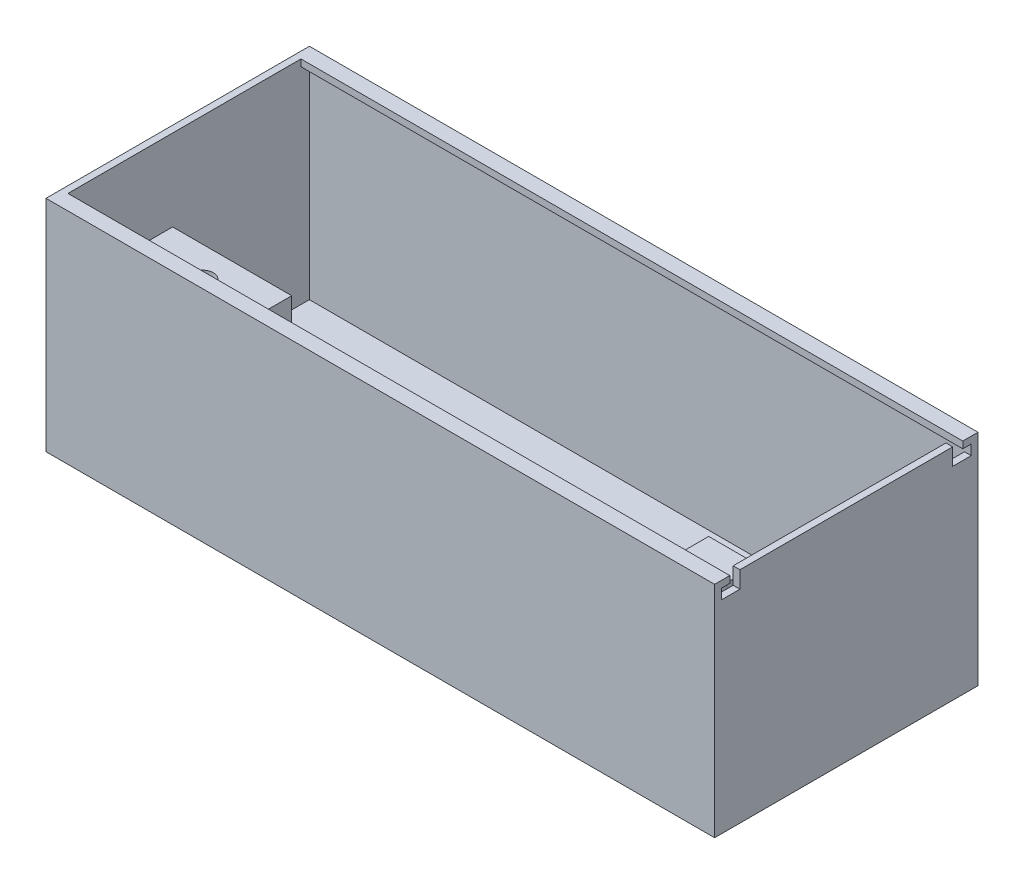
SolidWorks part; units mm, degrees
material "ABS"
ref_plane "Front" through (0, 0, 0) normal (0, 0, 1) x (1, 0, 0)
ref_plane "Top" through (0, 0, 0) normal (0, 1, 0) x (1, 0, 0)
ref_plane "Right" through (0, 0, 0) normal (1, 0, 0) x (0, 0, -1)
sketch "Sketch2" plane through (0, 0, 0) normal (0, 1, 0) x (1, 0, 0)
  line L1 (-99, -39) -> (99, -39)
  line L2 (-99, -39) -> (-99, 39)
  line L3 (-99, 39) -> (99, 39)
  line L4 (99, -39) -> (99, 39)
  line L5 (-99, -39) -> (99, 39) construction
  line L6 (-99, 39) -> (99, -39) construction
  point P0 (0, 0)
  dimension "D1" = 78
  dimension "D2" = 198
extrude "Boss-Extrude1" add sketch "Sketch2" along normal blind 50 and the other way blind 15
shell "Shell1" thickness 2
fillet "Fillet1" [suppressed] radius 10
sketch "Sketch3" plane through (-97, 0, 0) normal (1, 0, 0) x (0, 0, -1)
  line L0 (0, -15) -> (0, 50) construction
  line L1 (-37, 50) -> (-34.5, 50)
  line L2 (-37, 50) -> (-37, 48)
  line L3 (-37, 48) -> (-34.5, 48)
  line L4 (-34.5, 50) -> (-34.5, 48)
  line L5 (39, -15) -> (-39, -15) construction
  line L6 (37, 50) -> (-37, 50) construction
  line L7 (34.5, 50) -> (34.5, 48)
  line L8 (37, 48) -> (34.5, 48)
  line L9 (37, 50) -> (37, 48)
  line L10 (37, 50) -> (34.5, 50)
  dimension "D1" = 2.5
  dimension "D2" = 2
extrude "Boss-Extrude2" add sketch "Sketch3" along normal up to next
sketch "Sketch4" plane through (97, 0, 0) normal (-1, 0, 0) x (0, 0, 1)
  line L0 (-37, 48) -> (-37, 45)
  line L1 (-37, 48) -> (-37, -13) construction
  line L2 (-37, 45) -> (-31.5, 45)
  line L3 (-31.5, 45) -> (-31.5, 50)
  line L4 (34.5, 50) -> (-34.5, 50) construction
  line L5 (-31.5, 50) -> (-34.5, 50)
  line L6 (-34.5, 50) -> (-34.5, 48)
  line L7 (-37, 48) -> (-34.5, 48) construction
  line L8 (-34.5, 48) -> (-34.5, 50) construction
  line L9 (-34.5, 48) -> (-37, 48)
  line L10 (0, -15) -> (0, 50) construction
  line L11 (39, -15) -> (-39, -15) construction
  line L12 (34.5, 48) -> (37, 48)
  line L13 (34.5, 50) -> (34.5, 48)
  line L14 (31.5, 50) -> (34.5, 50)
  line L15 (31.5, 45) -> (31.5, 50)
  line L16 (37, 45) -> (31.5, 45)
  line L17 (37, 48) -> (37, 45)
  dimension "D1" = 3
  dimension "D2" = 3
extrude "Cut-Extrude1" cut sketch "Sketch4" against normal up to next
sketch "Croquis1" plane through (0, -13, 0) normal (0, 1, 0) x (1, 0, 0)
  line L0 (97, -37) -> (97, 37) construction
  line L1 (97, -29.5) -> (61.735, -29.5)
  line L2 (97, -29.5) -> (97, -3.5)
  line L3 (97, -3.5) -> (61.735, -3.5)
  line L4 (61.735, -29.5) -> (61.735, -3.5)
  line L6 (-97, -37) -> (97, -37) construction
  dimension "D1" = 35.265
  dimension "D2" = 26
  dimension "D3" = 7.5
extrude "Saliente-Extruir1" add sketch "Croquis1" along normal blind 38.9
mirror "Simetría1" about plane through (0, 0, 0) normal (1, 0, 0) of "Saliente-Extruir1"
sketch "Croquis2" plane through (0, 25.9, 0) normal (0, 1, 0) x (1, 0, 0)
  line L0 (79.235, -12.375) -> (79.235, -20.625) construction
  line L1 (82.41, -12.375) -> (82.41, -20.625)
  line L2 (76.06, -12.375) -> (76.06, -20.625)
  line L3 (97, -29.5) -> (97, -3.5) construction
  line L4 (79.235, -23.8) -> (79.235, -29.5) construction
  line L5 (61.735, -29.5) -> (97, -29.5) construction
  arc A0 (82.41, -12.375) -> (76.06, -12.375) centre (79.235, -12.375) ccw
  arc A1 (76.06, -20.625) -> (82.41, -20.625) centre (79.235, -20.625) ccw
  point P2 (79.235, -16.5)
  point P7 (79.235, -9.2)
  point P8 (79.235, -23.8)
  dimension "D1" = 14.6
  dimension "D2" = 6.35
  dimension "D3" = 14.59
  dimension "D4" = 5.7
extrude "Cortar-Extruir1" cut sketch "Croquis2" against normal blind 2
mirror "Simetría2" about plane through (0, 0, 0) normal (1, 0, 0) of "Cortar-Extruir1"
sketch "Croquis3" plane through (0, 23.9, 0) normal (0, 1, 0) x (1, 0, 0)
  line L0 (79.235, -13.2) -> (79.235, -19.8) construction
  line L1 (80.835, -13.2) -> (80.835, -19.8)
  line L2 (77.635, -13.2) -> (77.635, -19.8)
  line L3 (76.06, -12.375) -> (76.06, -20.625) construction
  arc A0 (80.835, -13.2) -> (77.635, -13.2) centre (79.235, -13.2) ccw
  arc A1 (77.635, -19.8) -> (80.835, -19.8) centre (79.235, -19.8) ccw
  point P3 (79.235, -16.5)
  point P11 (76.06, -16.5)
  dimension "D1" = 6.6
  dimension "D2" = 3.2
extrude "Cortar-Extruir2" cut sketch "Croquis3" against normal blind 30
mirror "Simetría3" about plane through (0, 0, 0) normal (1, 0, 0) of "Cortar-Extruir2"
sketch "Croquis5" plane through (61.735, 0, 0) normal (-1, 0, 0) x (0, 0, 1)
  line L0 (29.5, 25.9) -> (29.5, -13) construction
  line L1 (3.5, -13) -> (29.5, -13)
  line L2 (3.5, -13) -> (3.5, 2)
  line L3 (3.5, 2) -> (29.5, 2)
  line L4 (29.5, -13) -> (29.5, 2)
  dimension "D1" = 15
extrude "Cortar-Extruir3" cut sketch "Croquis5" against normal up to surface (35.265 mm away) up to face at (97, 23.3167, 5.5)
sketch "Croquis6" plane through (61.735, 0, 0) normal (-1, 0, 0) x (0, 0, 1)
  line L0 (29.5, 2) -> (3.5, 2) construction
  line L1 (10.5, 2) -> (22.5, 2)
  line L2 (10.5, 2) -> (10.5, 5)
  line L3 (10.5, 5) -> (22.5, 5)
  line L4 (22.5, 2) -> (22.5, 5)
  line L5 (3.5, 25.9) -> (3.5, 2) construction
  dimension "D1" = 12
  dimension "D2" = 7
  dimension "D3" = 3
extrude "Saliente-Extruir2" add sketch "Croquis6" along normal blind 3
sketch "Croquis7" plane through (-61.735, 0, 0) normal (1, 0, 0) x (0, 0, -1)
  line L0 (-29.5, 25.9) -> (-29.5, -13) construction
  line L1 (-3.5, -13) -> (-29.5, -13)
  line L2 (-3.5, -13) -> (-3.5, 2)
  line L3 (-3.5, 2) -> (-29.5, 2)
  line L4 (-29.5, -13) -> (-29.5, 2)
  dimension "D1" = 15
extrude "Cortar-Extruir4" cut sketch "Croquis7" against normal up to surface (35.265 mm away) up to face at (-97, 24.3167, 5.5)
mirror "Simetría7" about plane through (0, 0, 0) normal (1, 0, 0) of "Saliente-Extruir2"
